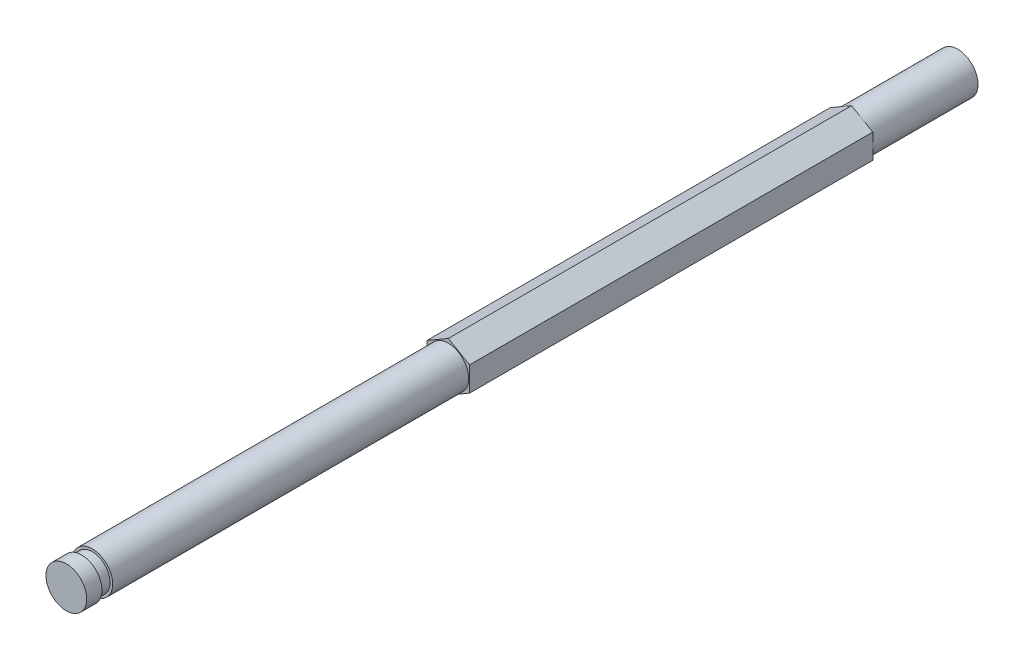
SolidWorks part; units mm, degrees
material "1060 Alloy"
ref_plane "Front Plane" through (0, 0, 0) normal (0, 0, 1) x (1, 0, 0)
ref_plane "Top Plane" through (0, 0, 0) normal (0, 1, 0) x (1, 0, 0)
ref_plane "Right Plane" through (0, 0, 0) normal (1, 0, 0) x (0, 0, -1)
sketch "Sketch2" plane through (0, 0, 0) normal (0, 0, 1) x (1, 0, 0)
  line L1 (0, 3.6662) -> (-3.175, 1.8331)
  line L2 (-3.175, 1.8331) -> (-3.175, -1.8331)
  line L3 (-3.175, -1.8331) -> (0, -3.6662)
  line L4 (0, -3.6662) -> (3.175, -1.8331)
  line L5 (3.175, -1.8331) -> (3.175, 1.8331)
  line L6 (3.175, 1.8331) -> (0, 3.6662)
  circle A0 centre (0, 0) radius 3.175 construction
  dimension "D1" = 6.35
extrude "Boss-Extrude1" add sketch "Sketch2" along normal blind 133.35
sketch "Sketch3" plane through (0, 0, 133.35) normal (0, 0, 1) x (1, 0, 0)
  circle A0 centre (0, 0) radius 3.048
  dimension "D1" = 6.096
extrude "Cut-Extrude1" cut sketch "Sketch3" against normal blind 57.15 flip side to cut
sketch "Sketch4" plane through (0, 0, 0) normal (0, 0, -1) x (-1, 0, 0)
  circle A0 centre (0, 0) radius 3.048
  dimension "D1" = 6.096
extrude "Cut-Extrude2" cut sketch "Sketch4" against normal blind 15.875 flip side to cut
ref_plane "Plane1" through (0, 0, 131.064) normal (0, 0, 1) x (1, 0, 0)
sketch "Sketch5" plane through (0, 0, 131.064) normal (0, 0, 1) x (1, 0, 0)
  circle A0 centre (0, 0) radius 2.667
  dimension "D1" = 5.334
extrude "Cut-Extrude3" cut sketch "Sketch5" against normal blind 1.6002 flip side to cut
